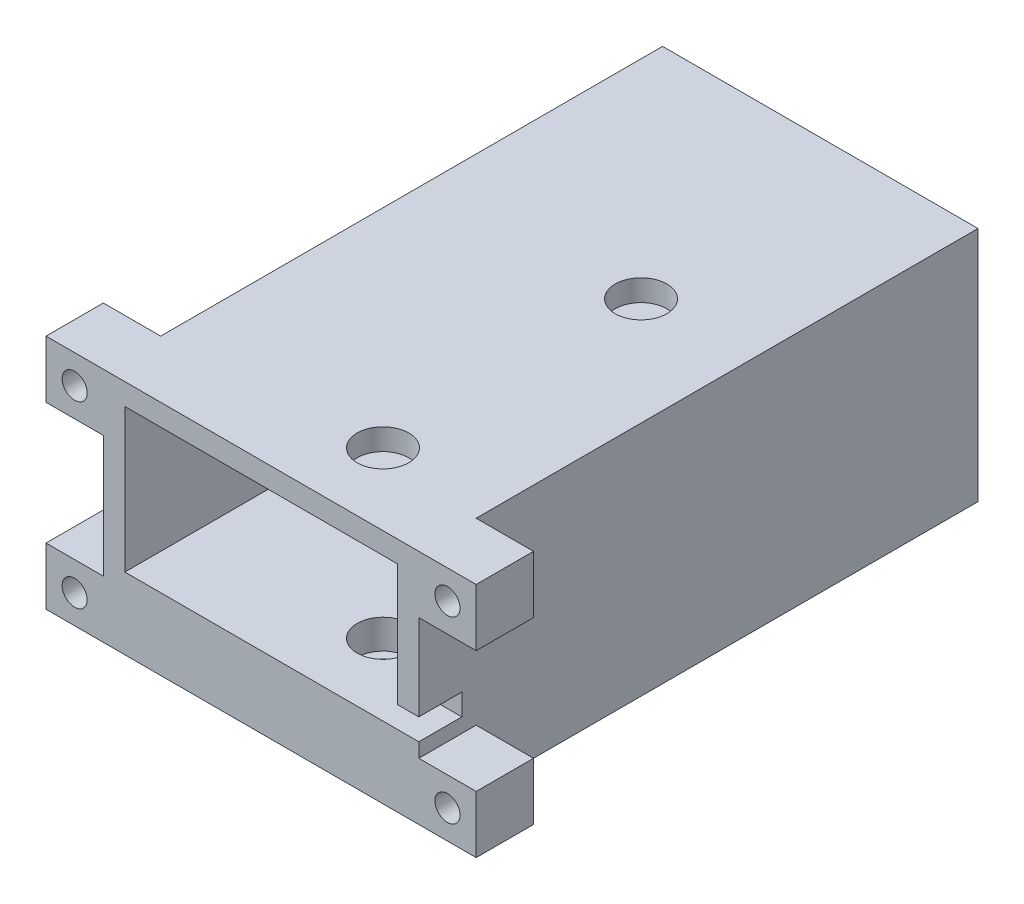
SolidWorks part; units mm, degrees
ref_plane "前基準面" through (0, 0, 0) normal (0, 0, 1) x (1, 0, 0)
ref_plane "上基準面" through (0, 0, 0) normal (0, 1, 0) x (1, 0, 0)
ref_plane "右基準面" through (0, 0, 0) normal (1, 0, 0) x (0, 0, -1)
sketch "草圖1" plane through (0, 0, 0) normal (0, 1, 0) x (1, 0, 0)
  line L1 (-22, 39) -> (22, 39)
  line L2 (-22, 39) -> (-22, -39)
  line L3 (-22, -39) -> (22, -39)
  line L4 (22, 39) -> (22, -39)
  line L5 (-22, 39) -> (22, -39) construction
  line L6 (-22, -39) -> (22, 39) construction
  point P0 (0, 0)
  dimension "D1" = 78
  dimension "D2" = 44
extrude "填料-伸長1" add sketch "草圖1" along normal blind 33
shell "薄殼1" thickness 3
sketch "草圖3" plane through (0, 10, 0) normal (0, 1, 0) x (1, 0, 0)
  line L0 (-22, -39) -> (22, -39) construction
  line L1 (22, -39) -> (22, 39) construction
  circle A0 centre (7, 7) radius 3.6
  circle A1 centre (7, -29) radius 3.6
  dimension "D1" = 7.2
  dimension "D2" = 36
  dimension "D3" = 10
  dimension "D4" = 15
extrude "除料-伸長1" cut sketch "草圖3" against normal blind 4.1
sketch "草圖4" plane through (0, 10, 0) normal (0, 1, 0) x (1, 0, 0)
  circle A0 centre (7, 7) radius 2.25
  circle A1 centre (7, -29) radius 2.25
  dimension "D1" = 4.5
extrude "除料-伸長2" cut sketch "草圖4" against normal up to next
sketch "草圖5" plane through (0, 0, 39) normal (0, 0, 1) x (1, 0, 0)
  line L0 (22, 33) -> (22, 0) construction
  line L1 (19, 10) -> (22, 10)
  line L2 (19, 10) -> (19, 13)
  line L3 (19, 13) -> (22, 13)
  line L4 (22, 10) -> (22, 13)
  dimension "D1" = 3
extrude "除料-伸長3" cut sketch "草圖5" against normal blind 6
sketch "草圖6" plane through (0, 0, 39) normal (0, 0, 1) x (1, 0, 0)
  line L0 (0, 0) -> (0, 15.8602) construction
  line L1 (-30, 25) -> (-22, 25)
  line L2 (-30, 25) -> (-30, 33)
  line L3 (-30, 33) -> (-22, 33)
  line L4 (-22, 25) -> (-22, 33)
  line L5 (-30, 25) -> (-22, 33) construction
  line L6 (-30, 33) -> (-22, 25) construction
  line L7 (-30, 8) -> (-22, 8)
  line L8 (-30, 8) -> (-30, 0)
  line L9 (-30, 0) -> (-22, 0)
  line L10 (-22, 8) -> (-22, 0)
  line L11 (-30, 8) -> (-22, 0) construction
  line L12 (-30, 0) -> (-22, 8) construction
  line L13 (30, 0) -> (22, 8) construction
  line L14 (30, 8) -> (22, 0) construction
  line L15 (30, 33) -> (22, 25) construction
  line L16 (30, 25) -> (22, 33) construction
  line L17 (22, 8) -> (22, 0)
  line L18 (30, 0) -> (22, 0)
  line L19 (30, 8) -> (30, 0)
  line L20 (30, 8) -> (22, 8)
  line L21 (22, 25) -> (22, 33)
  line L22 (30, 33) -> (22, 33)
  line L23 (30, 25) -> (30, 33)
  line L24 (30, 25) -> (22, 25)
  circle A0 centre (-26, 29) radius 1.75
  circle A1 centre (-26, 4) radius 1.75
  circle A2 centre (26, 29) radius 1.75
  circle A3 centre (26, 4) radius 1.75
  point P0 (-26, 29)
  point P6 (-26, 4)
  point P23 (26, 4)
  point P24 (26, 29)
  dimension "D2" = 3.5
  dimension "D1" = 8
extrude "填料-伸長2" add sketch "草圖6" against normal blind 8
sketch "草圖7" plane through (0, 0, 31) normal (0, 0, -1) x (-1, 0, 0)
  line L0 (0, 0) -> (0, 11.4673) construction
  line L1 (27.6166, 6.8) -> (29.2332, 4)
  line L2 (-22.7668, 29) -> (-24.3834, 31.8)
  line L3 (-24.3834, 31.8) -> (-27.6166, 31.8)
  line L4 (-27.6166, 31.8) -> (-29.2332, 29)
  line L5 (-29.2332, 29) -> (-27.6166, 26.2)
  line L6 (-27.6166, 26.2) -> (-24.3834, 26.2)
  line L7 (-24.3834, 26.2) -> (-22.7668, 29)
  line L8 (-29.2332, 4) -> (-27.6166, 1.2)
  line L9 (-27.6166, 1.2) -> (-24.3834, 1.2)
  line L10 (-24.3834, 1.2) -> (-22.7668, 4)
  line L11 (-22.7668, 4) -> (-24.3834, 6.8)
  line L12 (-24.3834, 6.8) -> (-27.6166, 6.8)
  line L13 (-27.6166, 6.8) -> (-29.2332, 4)
  line L14 (24.3834, 6.8) -> (27.6166, 6.8)
  line L15 (22.7668, 4) -> (24.3834, 6.8)
  line L16 (24.3834, 1.2) -> (22.7668, 4)
  line L17 (27.6166, 1.2) -> (24.3834, 1.2)
  line L18 (29.2332, 4) -> (27.6166, 1.2)
  line L19 (24.3834, 26.2) -> (22.7668, 29)
  line L20 (27.6166, 26.2) -> (24.3834, 26.2)
  line L21 (29.2332, 29) -> (27.6166, 26.2)
  line L22 (27.6166, 31.8) -> (29.2332, 29)
  line L23 (24.3834, 31.8) -> (27.6166, 31.8)
  line L24 (22.7668, 29) -> (24.3834, 31.8)
  circle A0 centre (-26, 29) radius 2.8 construction
  circle A1 centre (-26, 4) radius 2.8 construction
  circle A2 centre (26, 4) radius 2.8 construction
  circle A3 centre (26, 29) radius 2.8 construction
  dimension "D1" = 5.6
extrude "除料-伸長4" cut sketch "草圖7" against normal blind 2.6
sketch "草圖8" plane through (0, 0, -36) normal (0, 0, 1) x (1, 0, 0)
  circle A0 centre (0, 20) radius 5
  dimension "D1" = 10
  dimension "D2" = 20
extrude "除料-伸長5" cut sketch "草圖8" against normal up to next
sketch "草圖9" plane through (0, 33, 0) normal (0, 1, 0) x (1, 0, 0)
  circle A0 centre (7, 7) radius 3.6 construction
  circle A1 centre (7, 7) radius 3.6
  circle A2 centre (7, -29) radius 3.6 construction
  circle A3 centre (7, -29) radius 3.6
extrude "除料-伸長6" cut sketch "草圖9" against normal up to next
